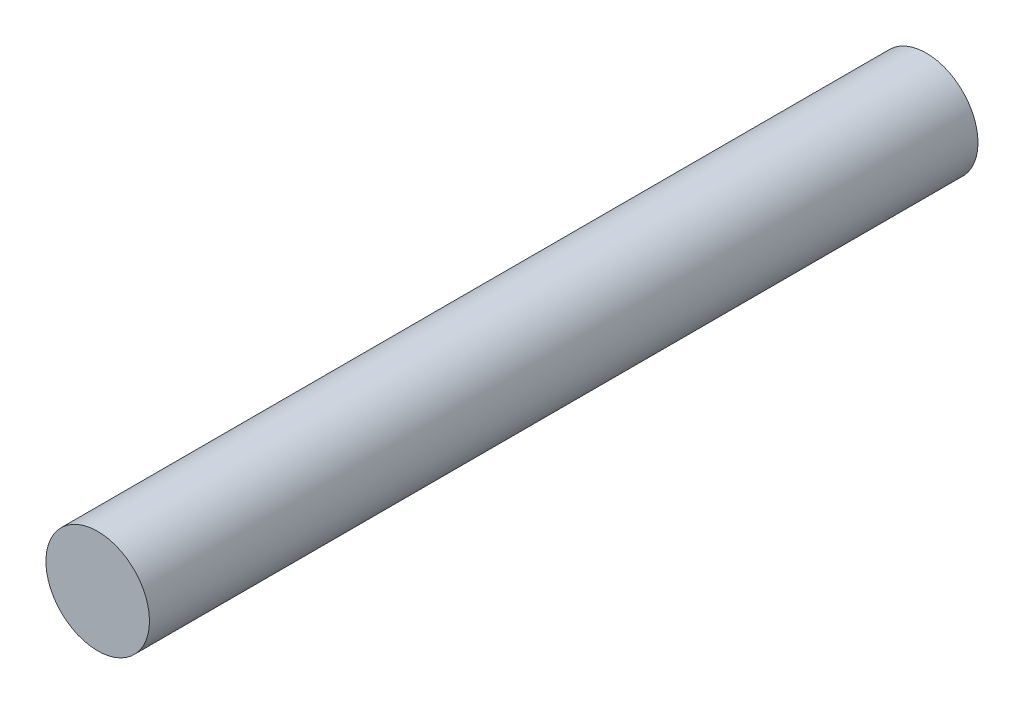
SolidWorks part; units mm, degrees
ref_plane "Front Plane" through (0, 0, 0) normal (0, 0, 1) x (1, 0, 0)
ref_plane "Top Plane" through (0, 0, 0) normal (0, 1, 0) x (1, 0, 0)
ref_plane "Right Plane" through (0, 0, 0) normal (1, 0, 0) x (0, 0, -1)
sketch "Sketch1" plane through (0, 0, 0) normal (0, 0, 1) x (1, 0, 0)
  circle A0 centre (0, 0) radius 1.5875
  dimension "D1" = 3.175
extrude "Boss-Extrude1" add sketch "Sketch1" along normal blind 25.4
